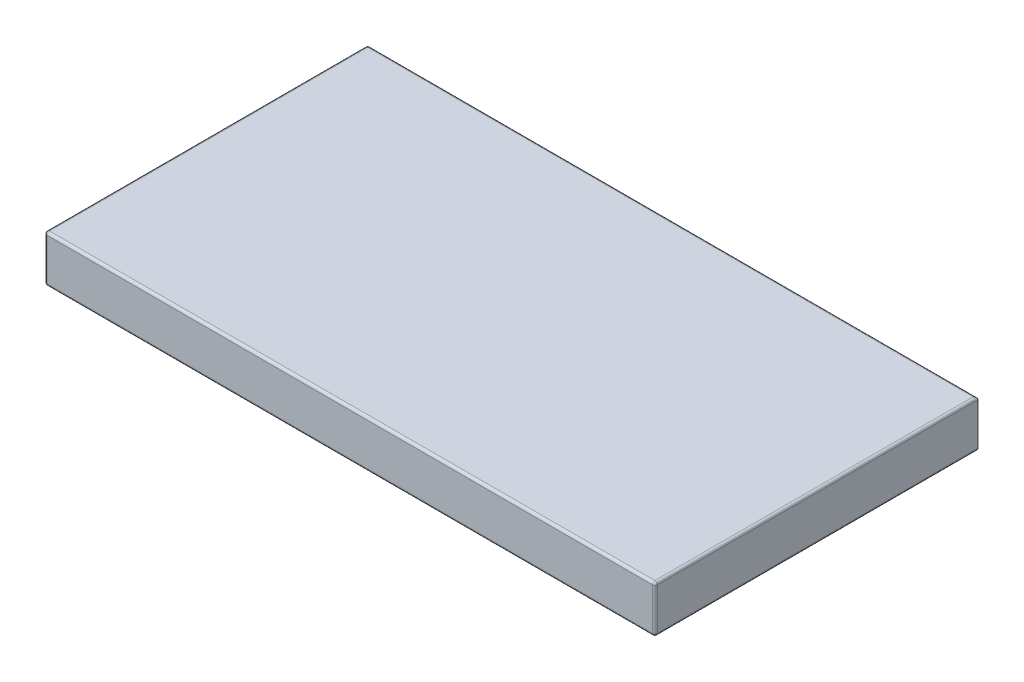
SolidWorks part; units mm, degrees
ref_plane "Спереди" through (0, 0, 0) normal (0, 0, 1) x (1, 0, 0)
ref_plane "Сверху" through (0, 0, 0) normal (0, 1, 0) x (1, 0, 0)
ref_plane "Справа" through (0, 0, 0) normal (1, 0, 0) x (0, 0, -1)
sketch "Эскиз1" plane through (0, 0, 0) normal (0, 1, 0) x (1, 0, 0)
  line L1 (0, 0) -> (122.3, 0)
  line L2 (0, 0) -> (0, -64.75)
  line L3 (0, -64.75) -> (122.3, -64.75)
  line L4 (122.3, 0) -> (122.3, -64.75)
  dimension "D1" = 122.3
  dimension "D2" = 64.75
extrude "Бобышка-Вытянуть1" add sketch "Эскиз1" along normal blind 9.4
fillet "Скругление1" radius 0.5 11 edges at (0, 4.7, 0) (122.3, 0, 32.375) (61.15, 0, 0) (0, 0, 32.375) (0, 4.7, 64.75) (122.3, 4.7, 64.75) (61.15, 0, 64.75) (61.15, 9.4, 0) (122.3, 9.4, 32.375) (61.15, 9.4, 64.75) (0, 9.4, 32.375)
